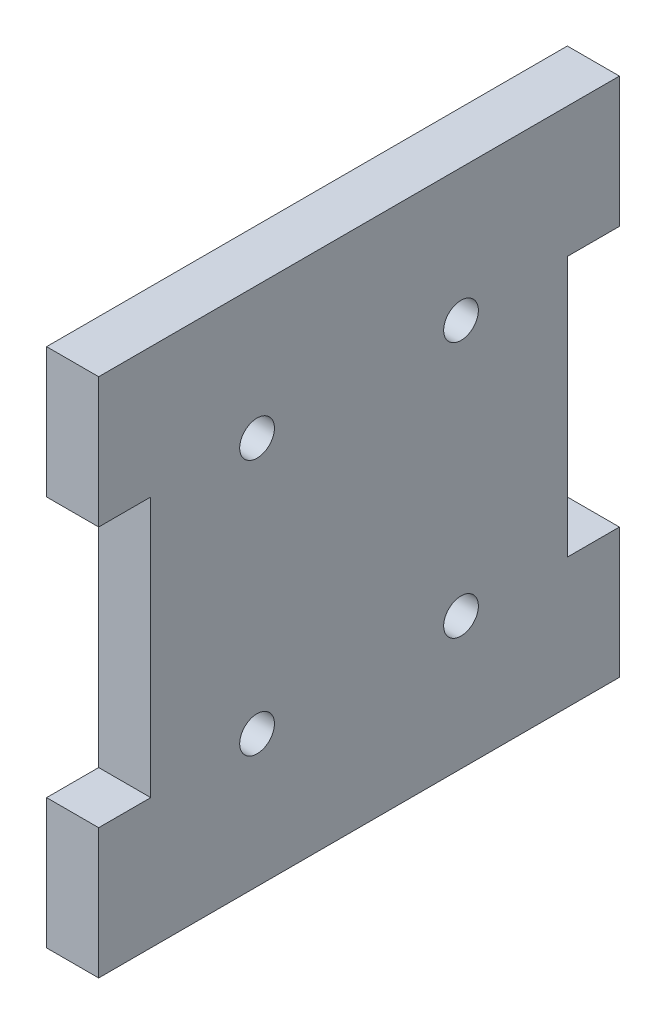
SolidWorks part; units mm, degrees
ref_plane "Front Plane" through (0, 0, 0) normal (0, 0, 1) x (1, 0, 0)
ref_plane "Top Plane" through (0, 0, 0) normal (0, 1, 0) x (1, 0, 0)
ref_plane "Right Plane" through (0, 0, 0) normal (1, 0, 0) x (0, 0, -1)
sketch "Sketch1" plane through (0, 0, 0) normal (1, 0, 0) x (0, 0, -1)
  line L1 (0, 0) -> (60, 0)
  line L2 (0, 0) -> (0, -60)
  line L3 (0, -60) -> (60, -60)
  line L4 (60, 0) -> (60, -60)
  point P4 (0, 0)
  dimension "D1" = 60
extrude "Boss-Extrude1" add sketch "Sketch1" along normal blind 6
sketch "Sketch2" plane through (6, 0, 0) normal (1, 0, 0) x (0, 0, -1)
  line L0 (0, 0) -> (0, -60) construction
  line L1 (0, -15) -> (6, -15)
  line L2 (0, -15) -> (0, -45)
  line L3 (0, -45) -> (6, -45)
  line L4 (6, -15) -> (6, -45)
  line L5 (60, 0) -> (0, 0) construction
  line L6 (0, -60) -> (60, -60) construction
  line L7 (30, 0) -> (30, -24.6698) construction
  line L8 (60, -45) -> (54, -45)
  line L9 (54, -15) -> (54, -45)
  line L10 (60, -15) -> (54, -15)
  line L11 (60, -15) -> (60, -45)
  dimension "D1" = 6
  dimension "D2" = 15
  dimension "D3" = 15
extrude "Cut-Extrude1" cut sketch "Sketch2" against normal blind 6
sketch "Sketch3" plane through (6, 0, 0) normal (1, 0, 0) x (0, 0, -1)
  line L0 (54, -15) -> (54, -45) construction
  line L1 (18.25, -15.25) -> (41.75, -15.25) construction
  line L2 (18.25, -15.25) -> (18.25, -44.75) construction
  line L3 (18.25, -44.75) -> (41.75, -44.75) construction
  line L4 (41.75, -15.25) -> (41.75, -44.75) construction
  line L5 (18.25, -15.25) -> (41.75, -44.75) construction
  line L6 (18.25, -44.75) -> (41.75, -15.25) construction
  line L7 (60, 0) -> (0, 0) construction
  circle A0 centre (18.25, -15.25) radius 2
  circle A1 centre (41.75, -15.25) radius 2
  circle A2 centre (41.75, -44.75) radius 2
  circle A3 centre (18.25, -44.75) radius 2
  point P0 (30, -30)
  point P8 (54, -30)
  point P11 (30, 0)
  dimension "D3" = 4
  dimension "D4" = 4
  dimension "D5" = 4
  dimension "D6" = 4
  dimension "D1" = 23.5
  dimension "D2" = 29.5
extrude "Cut-Extrude2" cut sketch "Sketch3" against normal blind 6
